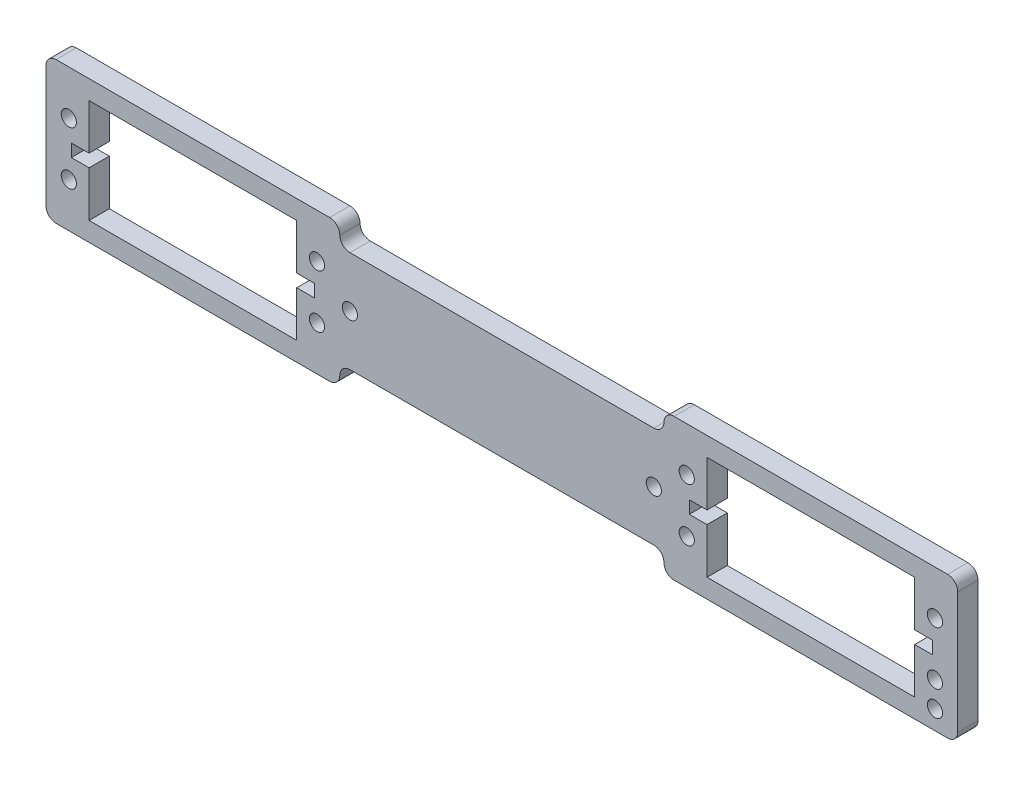
SolidWorks part; units mm, degrees
material "Beech"
ref_plane "Front Plane" through (0, 0, 0) normal (0, 0, 1) x (1, 0, 0)
ref_plane "Top Plane" through (0, 0, 0) normal (0, 1, 0) x (1, 0, 0)
ref_plane "Right Plane" through (0, 0, 0) normal (1, 0, 0) x (0, 0, -1)
sketch "Sketch1" plane through (0, 0, 0) normal (0, 0, 1) x (1, 0, 0)
  line L0 (0, 2) -> (0, 26)
  line L1 (2, 28) -> (56, 28)
  line L2 (178, 28) -> (124, 28)
  line L3 (120, 24) -> (60, 24)
  line L4 (8.5, 3.75) -> (8.5, 12.75)
  line L5 (49.5, 3.75) -> (8.5, 3.75)
  line L6 (49.5, 24.25) -> (49.5, 15.25)
  line L7 (8.5, 24.25) -> (49.5, 24.25)
  line L8 (130.5, 3.75) -> (130.5, 12.75)
  line L9 (171.5, 3.75) -> (130.5, 3.75)
  line L10 (171.5, 24.25) -> (171.5, 15.25)
  line L11 (130.5, 24.25) -> (171.5, 24.25)
  line L12 (2, 0) -> (56, 0)
  line L13 (180, 2) -> (180, 26)
  line L14 (178, 0) -> (124, 0)
  line L15 (120, 4) -> (60, 4)
  line L16 (175, 12.75) -> (175, 15.25)
  line L17 (175, 15.25) -> (171.5, 15.25)
  line L18 (175, 12.75) -> (171.5, 12.75)
  line L19 (53, 12.75) -> (53, 15.25)
  line L20 (53, 15.25) -> (49.5, 15.25)
  line L21 (53, 12.75) -> (49.5, 12.75)
  line L22 (5, 12.75) -> (5, 15.25)
  line L23 (5, 15.25) -> (8.5, 15.25)
  line L24 (5, 12.75) -> (8.5, 12.75)
  line L25 (127, 12.75) -> (127, 15.25)
  line L26 (127, 15.25) -> (130.5, 15.25)
  line L27 (127, 12.75) -> (130.5, 12.75)
  line L28 (8.5, 15.25) -> (8.5, 24.25)
  line L29 (49.5, 12.75) -> (49.5, 3.75)
  line L30 (130.5, 15.25) -> (130.5, 24.25)
  line L31 (171.5, 12.75) -> (171.5, 3.75)
  arc A0 (2, 28) -> (0, 26) centre (2, 26) ccw
  arc A1 (58, 26) -> (56, 28) centre (56, 26) ccw
  arc A2 (58, 26) -> (60, 24) centre (60, 26) ccw
  arc A3 (124, 28) -> (122, 26) centre (124, 26) ccw
  arc A4 (120, 24) -> (122, 26) centre (120, 26) ccw
  arc A5 (180, 26) -> (178, 28) centre (178, 26) ccw
  circle A6 centre (53.5, 19.25) radius 1.5
  circle A7 centre (53.5, 8.75) radius 1.5
  circle A8 centre (4.5, 19.25) radius 1.5
  circle A9 centre (4.5, 8.75) radius 1.5
  circle A10 centre (175.5, 19.25) radius 1.5
  circle A11 centre (175.5, 8.75) radius 1.5
  circle A12 centre (126.5, 19.25) radius 1.5
  circle A13 centre (126.5, 8.75) radius 1.5
  arc A14 (0, 2) -> (2, 0) centre (2, 2) ccw
  arc A15 (56, 0) -> (58, 2) centre (56, 2) ccw
  arc A16 (60, 4) -> (58, 2) centre (60, 2) ccw
  arc A17 (178, 0) -> (180, 2) centre (178, 2) ccw
  arc A18 (122, 2) -> (124, 0) centre (124, 2) ccw
  arc A19 (122, 2) -> (120, 4) centre (120, 2) ccw
  circle A20 centre (60, 14) radius 1.5
  circle A21 centre (120, 14) radius 1.5
  circle A22 centre (175.5, 3.75) radius 1.5
extrude "Boss-Extrude1" add sketch "Sketch1" along normal blind 4
